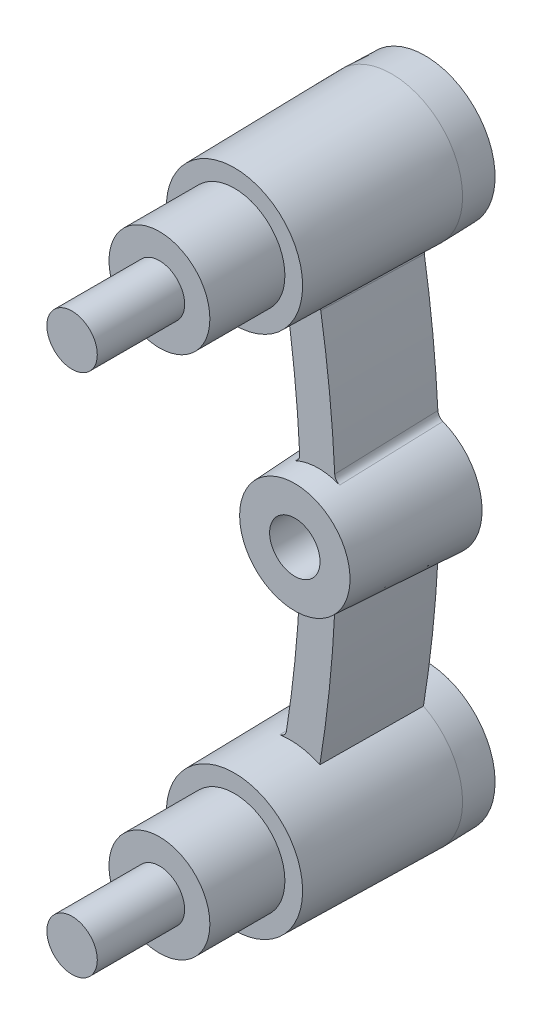
SolidWorks part; units mm, degrees
ref_plane "Front Plane" through (0, 0, 0) normal (0, 0, 1) x (1, 0, 0)
ref_plane "Top Plane" through (0, 0, 0) normal (0, 1, 0) x (1, 0, 0)
ref_plane "Right Plane" through (0, 0, 0) normal (1, 0, 0) x (0, 0, -1)
sketch "Sketch1" plane through (0, 0, 0) normal (0, 0, 1) x (1, 0, 0)
  line L0 (0, 16.5) -> (0, -16.5) construction
  circle A0 centre (0, -16.5) radius 4.5
  circle A1 centre (0, 16.5) radius 4.5
  point P5 (0, 0)
  dimension "D2" = 9
  dimension "D1" = 33
extrude "Boss-Extrude1" add sketch "Sketch1" along normal blind 12 draft 1
sketch "Sketch2" plane through (0, 0, 0) normal (0, 0, 1) x (1, 0, 0)
  arc A0 (0, 16.5) -> (0, -16.5) centre (-74.725, 0) cw
  dimension "D1" = 76.525
extrude "Extrude-Thin1" add sketch "Sketch2" along normal blind 8.5 draft 1 thin thin type mid plane wall 2.5
sketch "Sketch3" plane through (0, 0, 12) normal (0, 0, 1) x (1, 0, 0)
  circle A0 centre (0, 16.5) radius 3.175
  circle A1 centre (0, -16.5) radius 3.175
  dimension "D1" = 6.35
extrude "Boss-Extrude2" add sketch "Sketch3" along normal blind 4.7235
sketch "Sketch4" plane through (0, 0, 16.7235) normal (0, 0, 1) x (1, 0, 0)
  circle A0 centre (0, 16.5) radius 1.5875
  circle A1 centre (0, -16.5) radius 1.5875
  dimension "D1" = 3.175
extrude "Boss-Extrude3" add sketch "Sketch4" along normal blind 5.5
sketch "Sketch5" plane through (0, 0, 0) normal (0, 0, -1) x (-1, 0, 0)
  line L0 (-0.55, 0) -> (-3.05, 0) construction
  arc A0 (0.4158, 12.0192) -> (0.4158, -12.0192) centre (74.725, 0) ccw construction
  arc A1 (-2.0407, 12.4893) -> (-2.0407, -12.4893) centre (74.725, 0) ccw construction
  circle A2 centre (-1.8, 0) radius 4
  dimension "D1" = 8
extrude "Boss-Extrude4" add sketch "Sketch5" against normal blind 10 draft 3
sketch "Sketch6" plane through (0, 0, 0) normal (0, 0, -1) x (-1, 0, 0)
  circle A0 centre (-1.8, 0) radius 1.5875
  dimension "D1" = 3.175
extrude "Cut-Extrude2" cut sketch "Sketch6" against normal through all
sketch "Sketch8" plane through (0, 0, 0) normal (0, 0, -1) x (-1, 0, 0)
  line L1 (10.3468, -24.2884) -> (-13.9468, -24.2884)
  line L2 (10.3468, -24.2884) -> (10.3468, 24.2884)
  line L3 (10.3468, 24.2884) -> (-13.9468, 24.2884)
  line L4 (-13.9468, -24.2884) -> (-13.9468, 24.2884)
  line L5 (10.3468, -24.2884) -> (-13.9468, 24.2884) construction
  line L6 (10.3468, 24.2884) -> (-13.9468, -24.2884) construction
  point P0 (-1.8, 0)
extrude "Cut-Extrude3" cut sketch "Sketch8" against normal blind 2.1016 draft 3
fillet "Fillet3" radius 0.5 6 edges at (0.5908, 3.4357, 6.8261) (2.8525, 3.4869, 6.8261)
sketch "Sketch9" plane through (0, 0, 2.1016) normal (0, 0, -1) x (-1, 0, 0)
  arc A0 (0.3841, 12.0532) -> (-2.2928, 12.6706) centre (0, 16.5) ccw construction
  arc A1 (-2.0001, -12.5099) -> (0.7363, -12.0978) centre (0, -16.5) ccw construction
  arc A2 (0.3841, 12.0532) -> (-2.2928, 12.6706) centre (0, 16.5) ccw
  arc A3 (-2.0001, -12.5099) -> (0.7363, -12.0978) centre (0, -16.5) ccw
  arc A4 (-2.2928, 12.6706) -> (0.3841, 12.0532) centre (0, 16.5) ccw
  arc A5 (-2.0001, -12.5099) -> (0.7363, -12.0978) centre (0, -16.5) cw
extrude "Boss-Extrude5" add sketch "Sketch9" along normal blind 2.1016 draft 1.5
sketch "Sketch10" plane through (0, 0, 0) normal (0, 0, -1) x (-1, 0, 0)
  line L1 (4.2537, -11.6304) -> (-7.8537, -11.6304)
  line L2 (4.2537, -11.6304) -> (4.2537, 11.6304)
  line L3 (4.2537, 11.6304) -> (-7.8537, 11.6304)
  line L4 (-7.8537, -11.6304) -> (-7.8537, 11.6304)
  line L5 (4.2537, -11.6304) -> (-7.8537, 11.6304) construction
  line L6 (4.2537, 11.6304) -> (-7.8537, -11.6304) construction
  point P0 (-1.8, 0)
extrude "Boss-Extrude6" [suppressed] add sketch "Sketch10" against normal offset from surface (1.9016 mm away) 0.2 separate body
